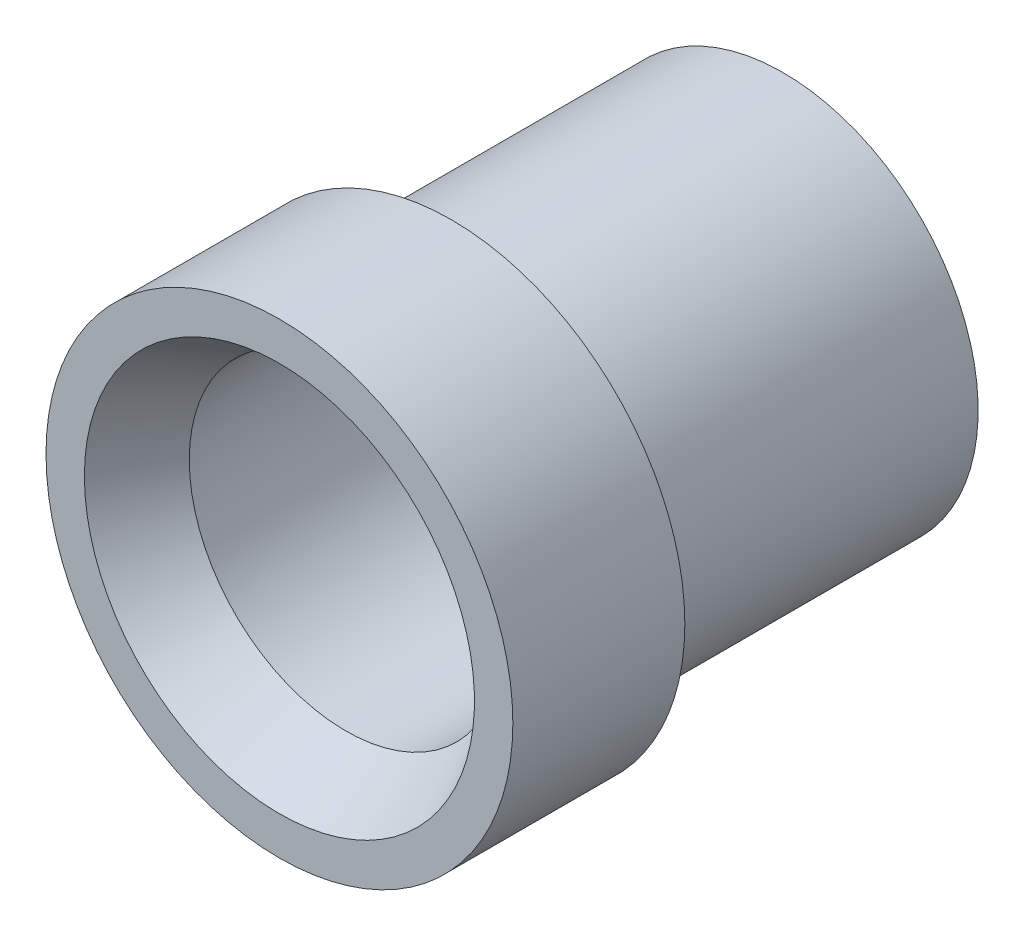
SolidWorks part; units mm, degrees
material "AISI Type 316L stainless steel"
ref_plane "Front" through (0, 0, 0) normal (0, 0, 1) x (1, 0, 0)
ref_plane "Top" through (0, 0, 0) normal (0, 1, 0) x (1, 0, 0)
ref_plane "Right" through (0, 0, 0) normal (1, 0, 0) x (0, 0, -1)
sketch "Sketch1" plane through (0, 0, 0) normal (1, 0, 0) x (0, 0, -1)
  line L0 (-5.207, 4.0323) -> (-3.8322, 3.2385)
  line L1 (5.207, 3.2385) -> (5.207, 4.0323)
  line L2 (5.207, 4.0323) -> (-1.651, 4.0323)
  line L3 (-1.651, 4.0323) -> (-1.651, 4.826)
  line L4 (-1.651, 4.826) -> (-5.207, 4.826)
  line L5 (-5.207, 4.826) -> (-5.207, 4.0323)
  line L6 (-3.8322, 3.2385) -> (5.207, 3.2385)
  line L7 (5.207, 0) -> (-5.207, 0) construction
  dimension "D1" = 30
  dimension "Length" = 10.414
  dimension "Band" = 3.556
  dimension "Max OD" = 9.652
  dimension "ID" = 6.477
revolve "Revolve1" add sketch "Sketch1" angle 360 about L7
